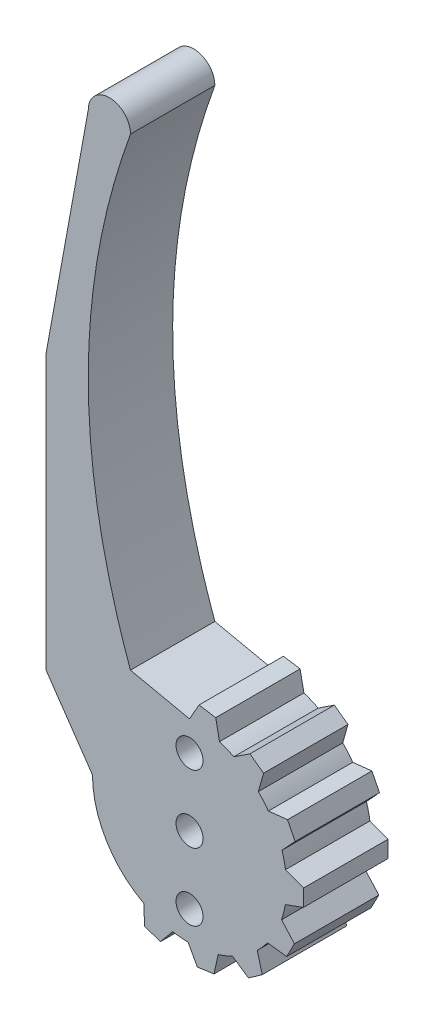
SolidWorks part; units mm, degrees
ref_plane "前基準面" through (0, 0, 0) normal (0, 0, 1) x (1, 0, 0)
ref_plane "上基準面" through (0, 0, 0) normal (0, 1, 0) x (1, 0, 0)
ref_plane "右基準面" through (0, 0, 0) normal (1, 0, 0) x (0, 0, -1)
sketch "草圖1" plane through (0, 0, 0) normal (0, 0, 1) x (1, 0, 0)
  line L0 (0, 0) -> (0, 55) construction
  line L1 (0, 27.5) -> (-5, 27.5) construction
  line L2 (0, 55) -> (-5, 55) construction
  line L3 (-5, 27.5) -> (-10, 27.5) construction
  line L4 (-5, 55) -> (-10, 27.5)
  line L5 (-10, 27.5) -> (-10, -5)
  line L6 (0, 0) -> (0, -13) construction
  line L7 (0, -13) -> (7, -13) construction
  line L8 (-10, -5) -> (-4.5, -13)
  line L9 (0, 0) -> (7, -1.5)
  line L10 (7, -1.5) -> (8.1242, 0.4902)
  line L11 (8.1242, 0.4902) -> (10.0996, 0.1774)
  line L12 (10.0996, 0.1774) -> (10.5537, -2.0629)
  line L13 (7, -1.5) -> (10.5537, -2.0629) construction
  line L14 (7, -1.5) -> (7, -13) construction
  line L15 (7, -13) -> (10.5537, -2.0629) construction
  line L16 (15.7699, -2.6879) -> (15.152, -4.8886)
  line L17 (14.1548, -1.5083) -> (15.7699, -2.6879)
  line L18 (12.2464, -2.7665) -> (14.1548, -1.5083)
  line L19 (12.2464, -2.7665) -> (7, -13) construction
  line L20 (7, -13) -> (15.152, -4.8886) construction
  line L21 (19.5085, -7.8244) -> (17.9547, -9.5009)
  line L22 (18.6095, -6.0379) -> (19.5085, -7.8244)
  line L23 (16.3373, -6.2869) -> (18.6095, -6.0379)
  line L24 (16.3373, -6.2869) -> (7, -13) construction
  line L25 (7, -13) -> (17.9547, -9.5009) construction
  line L26 (20.4921, -14.101) -> (18.3446, -14.8839)
  line L27 (20.5071, -12.101) -> (20.4921, -14.101)
  line L28 (18.3716, -11.286) -> (20.5071, -12.101)
  line L29 (18.3716, -11.286) -> (7, -13) construction
  line L30 (7, -13) -> (18.3446, -14.8839) construction
  line L31 (18.504, -20.135) -> (16.2358, -19.852)
  line L32 (19.4297, -18.3621) -> (18.504, -20.135)
  line L33 (17.9012, -16.6626) -> (19.4297, -18.3621)
  line L34 (17.9012, -16.6626) -> (7, -13) construction
  line L35 (7, -13) -> (16.2358, -19.852) construction
  line L36 (13.982, -24.5975) -> (12.0927, -23.3109)
  line L37 (15.6146, -23.4421) -> (13.982, -24.5975)
  line L38 (15.0297, -21.2325) -> (15.6146, -23.4421)
  line L39 (15.0297, -21.2325) -> (7, -13) construction
  line L40 (7, -13) -> (12.0927, -23.3109) construction
  line L41 (7.9222, -26.5055) -> (6.828, -24.4987)
  line L42 (9.9021, -26.2223) -> (7.9222, -26.5055)
  line L43 (10.3897, -23.9891) -> (9.9021, -26.2223)
  line L44 (10.3897, -23.9891) -> (7, -13) construction
  line L45 (7, -13) -> (6.828, -24.4987) construction
  line L46 (1.6593, -25.4389) -> (1.6011, -23.1539)
  line L47 (3.5503, -26.0901) -> (1.6593, -25.4389)
  line L48 (5.003, -24.3253) -> (3.5503, -26.0901)
  line L49 (5.003, -24.3253) -> (7, -13) construction
  line L50 (7, -13) -> (1.6011, -23.1539) construction
  line L51 (12.2464, -2.7665) -> (15.152, -4.8886) construction
  line L52 (16.3373, -6.2869) -> (17.9547, -9.5009) construction
  line L53 (18.3716, -11.286) -> (18.3446, -14.8839) construction
  line L54 (17.9012, -16.6626) -> (16.2358, -19.852) construction
  line L55 (15.0297, -21.2325) -> (12.0927, -23.3109) construction
  line L56 (10.3897, -23.9891) -> (6.828, -24.4987) construction
  line L57 (5.003, -24.3253) -> (1.6011, -23.1539) construction
  arc A0 (-5, 55) -> (0, 55) centre (-2.5, 55) cw
  circle A1 centre (7, -13) radius 11.5
  spline S0 degree 2 poles (0, 55) (-10, 27.5) (0, 0) knots 0 0 0 1 1 1
  dimension "D6" = 13
  dimension "D8" = 23
  dimension "D1" = 55
  dimension "D2" = 5
  dimension "D3" = 5
  dimension "D4" = 5
  dimension "D5" = 5
  dimension "D7" = 7
  dimension "D9" = 13.5
  dimension "D10" = 18
  dimension "D11" = 2
  dimension "D12" = 8
extrude "填料-伸長1" add sketch "草圖1" along normal blind 10 contours S0 A0 L4 L5 L8 A1 L9 | A1 | A1 L12 L11 L10 | A1 L16 L17 L18 | A1 L21 L22 L23 | A1 L26 L27 L28 | A1 L31 L32 L33 | A1 L36 L37 L38 | A1 L41 L42 L43 | A1 L46 L47 L48
sketch "草圖2" plane through (0, 0, 10) normal (0, 0, 1) x (1, 0, 0)
  line L0 (7, -5) -> (7, -21) construction
  circle A0 centre (7, -5) radius 1.6
  circle A1 centre (7, -21) radius 1.6
  circle A3 centre (7, -13) radius 1.6
  arc A4 (-4.5, -13) -> (1.6011, -23.1539) centre (7, -13) ccw construction
  dimension "D1" = 3.2
  dimension "D2" = 3.2
  dimension "D3" = 16
  dimension "D4" = 3.2
extrude "除料-伸長1" cut sketch "草圖2" against normal blind 10
